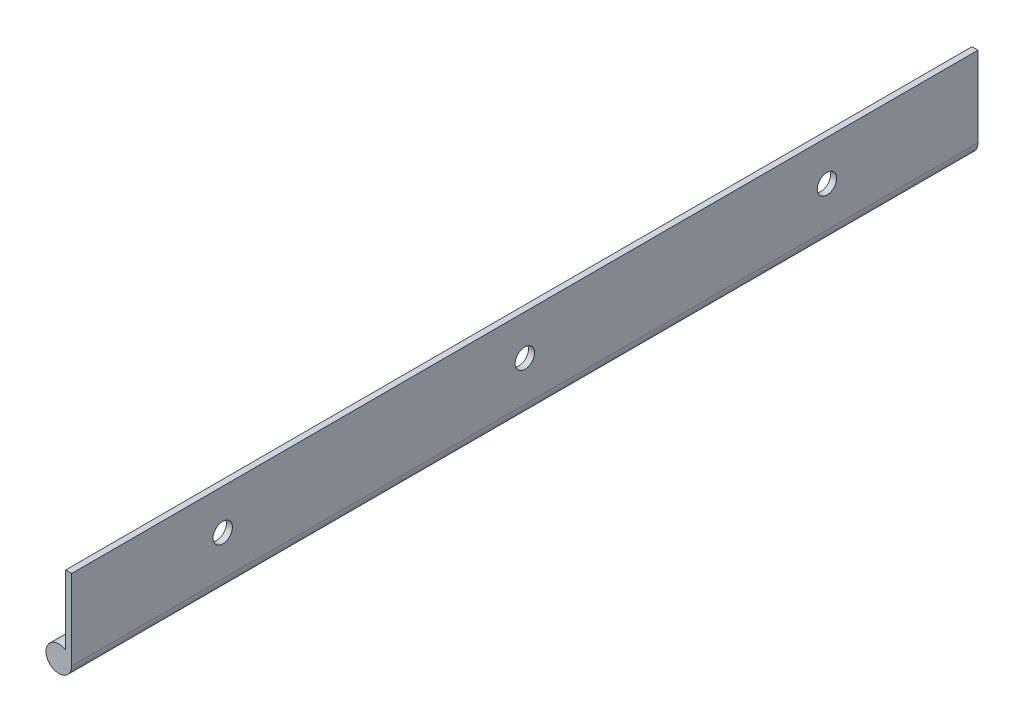
SolidWorks part; units mm, degrees
material "6061-T6 (SS)"
ref_plane "Front Plane" through (0, 0, 0) normal (0, 0, 1) x (1, 0, 0)
ref_plane "Top Plane" through (0, 0, 0) normal (0, 1, 0) x (1, 0, 0)
ref_plane "Right Plane" through (0, 0, 0) normal (1, 0, 0) x (0, 0, -1)
sketch "Sketch2" plane through (0, 0, 0) normal (0, 0, 1) x (1, 0, 0)
  line L2 (-0.508, -4.9153) -> (-0.508, 6.7469)
  line L3 (-0.508, 6.7469) -> (0.508, 6.7469)
  line L4 (0.508, -6.7469) -> (0.508, 6.7469)
  arc A0 (-0.508, -4.9153) -> (0.508, -6.7469) centre (-1.651, -6.7469) ccw
  point P0 (0, 0)
  dimension "D3" = 4.318
  dimension "D1" = 13.4937
  dimension "D2" = 1.016
extrude "Boss-Extrude2" add sketch "Sketch2" along normal blind 152.4
sketch "Sketch3" plane through (0.508, 0, 0) normal (1, 0, 0) x (0, 0, -1)
  line L0 (0, 0) -> (-152.4, 0) construction
  line L1 (-152.4, -6.7469) -> (-152.4, 6.7469) construction
  line L2 (-152.4, 6.7469) -> (-152.4, -4.9153) construction
  point P5 (-127, 0)
  point P6 (-76.2, 0)
  point P7 (-25.4, 0)
  dimension "D1" = 25.4
  dimension "D2" = 50.8
  dimension "D3" = 50.8
hole_wizard "#4 Clearance Hole1" positions "Sketch18" profile "Sketch17" hole size "#4" standard "ANSI Inch"
sketch "Sketch18" plane through (-0.508, 0, 0) normal (-1, 0, 0) x (0, 0, 1)
  point P0 (25.4, 0)
  point P2 (76.2, 0)
  point P4 (127, 0)
sketch "Sketch17" plane through (-0.508, 0, 25.4) normal (0, 1, 0) x (0, 0, 1)
  line L0 (0, 0) -> (0, 2.5046)
  line L1 (0, 2.5046) -> (1.6319, 1.524)
  line L2 (1.6319, 1.524) -> (1.6319, 0)
  line L5 (1.6319, 0) -> (0, 0)
  line L10 (0, 2.5046) -> (-1.6319, 1.524) construction
  line L11 (0, -6.35) -> (0, 107.95) construction
  dimension "Hole Dia." = 3.2639
  dimension "Hole Depth" = 1.524
  dimension "Drill Angle" = 118
